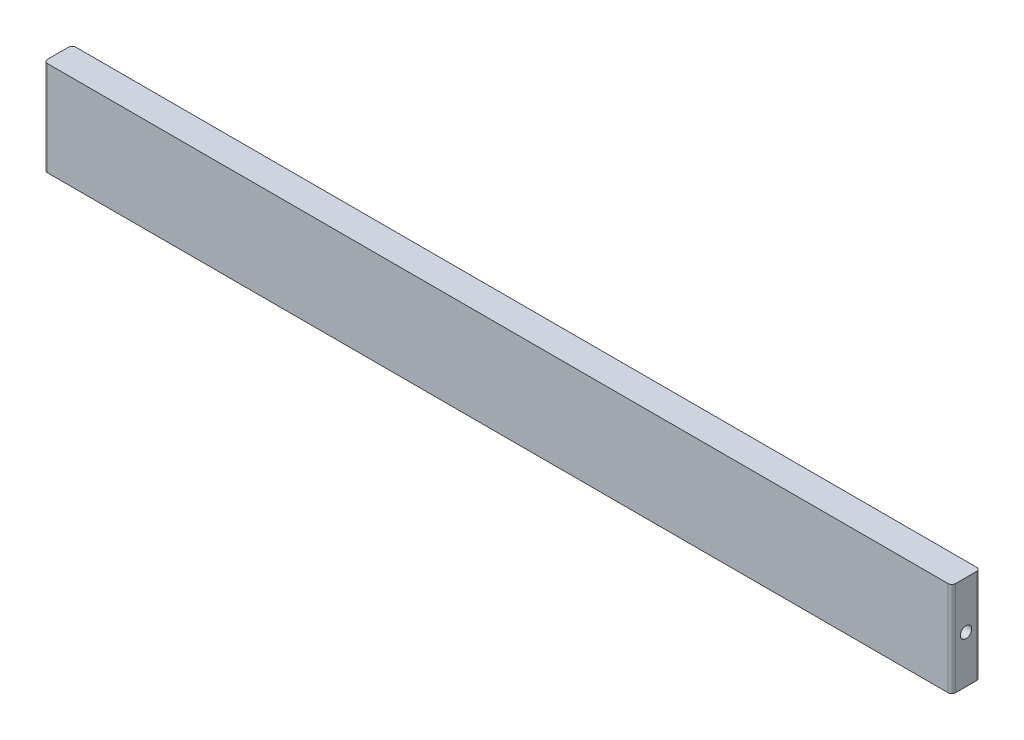
SolidWorks part; units mm, degrees
material "6061 Alloy"
ref_plane "Front Plane" through (0, 0, 0) normal (0, 0, 1) x (1, 0, 0)
ref_plane "Top Plane" through (0, 0, 0) normal (0, 1, 0) x (1, 0, 0)
ref_plane "Right Plane" through (0, 0, 0) normal (1, 0, 0) x (0, 0, -1)
sketch "Sketch1" plane through (0, -21, 0) normal (0, 1, 0) x (1, 0, 0)
  line L0 (-152.4, -170) -> (152.4, -170)
  line L4 (-152.4, 179.525) -> (-152.4, -179.525)
  line L5 (-152.4, -179.525) -> (152.4, -179.525)
  line L7 (152.4, 179.525) -> (-152.4, 179.525)
  line L9 (-152.4, -179.525) -> (152.4, -179.525)
  line L11 (152.4, 179.525) -> (-152.4, 179.525)
  line L17 (-152.4, 179.525) -> (-152.4, -179.525)
  line L23 (152.4, -179.525) -> (152.4, 179.525)
  line L24 (152.4, -179.525) -> (152.4, 179.525)
  line M6 (-152.4, 179.525) -> (-152.4, -179.525)
  line M7 (-152.4, -179.525) -> (152.4, -179.525)
  line M8 (152.4, -179.525) -> (152.4, 179.525)
  circle M23 centre (127, -174.7625) radius 2.4574
  circle M24 centre (42.3333, -174.7625) radius 2.4574
  circle M25 centre (-42.3333, -174.7625) radius 2.4574
  circle M26 centre (-127, -174.7625) radius 2.4574
  dimension "D2" = 9.525
  dimension "D1" = 0
extrude "Boss-Extrude1" add sketch "Sketch1" along normal blind 31.75 contours L0 M6 M7 M8 | M26 | M25 | M24 | M23
hole_wizard "#10-24 Tapped Hole1" positions "Sketch2" profile "Sketch3" tap size "#10-24" standard "ANSI Inch"
sketch "Sketch2" plane through (0, -21, 0) normal (0, -1, 0) x (-1, 0, 0)
  point P0 (-127, -174.7625)
  point P3 (-42.3333, -174.7625)
  point P6 (127, -174.7625)
  point P9 (42.3333, -174.7625)
sketch "Sketch3" plane through (127, -21, 174.7625) normal (1, 0, 0) x (0, 0, -1)
  line L0 (0, 0) -> (0, 20.1908)
  line L1 (0, 20.1908) -> (1.8986, 19.05)
  line L2 (1.8986, 19.05) -> (1.8986, 0)
  line L5 (1.8986, 0) -> (0, 0)
  line L10 (0, 20.1908) -> (-1.8987, 19.05) construction
  line L11 (0, -6.35) -> (0, 107.95) construction
  dimension "Tap Drill Dia." = 3.7973
  dimension "Tap Drill Depth" = 19.05
  dimension "Drill Angle" = 118
cosmetic thread "Hole Thread1" parameters "D1"=15.24, "D2"=4.826
cosmetic thread "Hole Thread2" parameters "D1"=15.24, "D2"=4.826
cosmetic thread "Hole Thread3" parameters "D1"=15.24, "D2"=4.826
cosmetic thread "Hole Thread4" parameters "D1"=15.24, "D2"=4.826
hole_wizard "#10-24 Tapped Hole2" positions "Sketch4" profile "Sketch5" tap size "#10-24" standard "ANSI Inch"
sketch "Sketch4" plane through (152.4, 0, 0) normal (1, 0, 0) x (0, 0, -1)
  point P0 (-174.7625, -5.125)
sketch "Sketch5" plane through (152.4, -5.125, 174.7625) normal (0, 1, 0) x (0, 0, -1)
  line L0 (0, 0) -> (0, 20.1908)
  line L1 (0, 20.1908) -> (1.8986, 19.05)
  line L2 (1.8986, 19.05) -> (1.8986, 0)
  line L5 (1.8986, 0) -> (0, 0)
  line L10 (0, 20.1908) -> (-1.8986, 19.05) construction
  line L11 (0, -6.35) -> (0, 107.95) construction
  dimension "Tap Drill Dia." = 3.7973
  dimension "Tap Drill Depth" = 19.05
  dimension "Drill Angle" = 118
cosmetic thread "Hole Thread5" parameters "D1"=15.24, "D2"=4.826
mirror "Mirror1" about plane through (0, 0, 0) normal (1, 0, 0) of "#10-24 Tapped Hole2"
cosmetic thread "Hole Thread6" parameters "D1"=15.24, "D2"=4.826
fillet "Fillet1" radius 1.27 4 edges at (152.4, -5.125, 170) (152.4, -5.125, 179.525) (-152.4, -5.125, 170) (-152.4, -5.125, 179.525)
